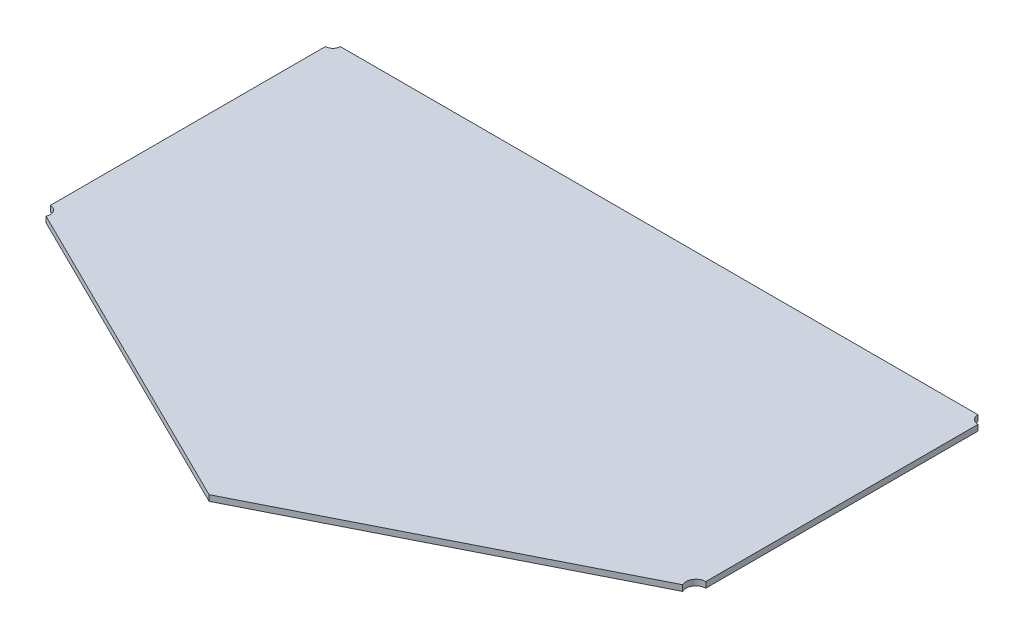
SolidWorks part; units mm, degrees
ref_plane "Front Plane" through (0, 0, 0) normal (0, 0, 1) x (1, 0, 0)
ref_plane "Top Plane" through (0, 0, 0) normal (0, 1, 0) x (1, 0, 0)
ref_plane "Right Plane" through (0, 0, 0) normal (1, 0, 0) x (0, 0, -1)
sketch "Sketch1" plane through (0, 0, 0) normal (0, 1, 0) x (1, 0, 0)
  line L1 (-234.4988, -2.7723) -> (-7.347, -115.1588)
  line L2 (-7.347, -115.1588) -> (215.4901, -2.7723)
  line L3 (-234.5044, -2.7633) -> (-234.5044, 197.2177)
  line L4 (-234.4944, 197.2277) -> (215.4856, 197.2277)
  line L5 (215.4956, 197.2177) -> (215.4956, -2.7634)
  arc A0 (-234.5044, 197.2177) -> (-234.4944, 197.2277) centre (-234.4944, 197.2177) cw
  arc A1 (215.4856, 197.2277) -> (215.4956, 197.2177) centre (215.4856, 197.2177) cw
  arc A2 (215.4956, -2.7634) -> (215.4901, -2.7723) centre (215.4856, -2.7634) cw
  arc A3 (-234.5044, -2.7633) -> (-234.4988, -2.7723) centre (-234.4944, -2.7633) ccw
  point P2 (0, 0)
  point P12 (215.4956, -2.7695)
  point P15 (-234.5044, -2.7695)
  dimension "D4" = 0.01
  dimension "D1" = 253.44
  dimension "D2" = 249.58
  dimension "D3" = 450
  dimension "D5" = 200
extrude "Boss-Extrude1" add sketch "Sketch1" along normal blind 4
sketch "Sketch3" plane through (0, 4, 0) normal (0, 1, 0) x (1, 0, 0)
  circle A0 centre (-234.4944, -2.7633) radius 5.4704
  circle A1 centre (-234.4944, 197.2177) radius 5.1364
  circle A2 centre (215.4856, 197.2177) radius 5.7436
  circle A3 centre (215.4856, -2.7634) radius 6.7793
extrude "Cut-Extrude2" cut sketch "Sketch3" against normal blind 85
